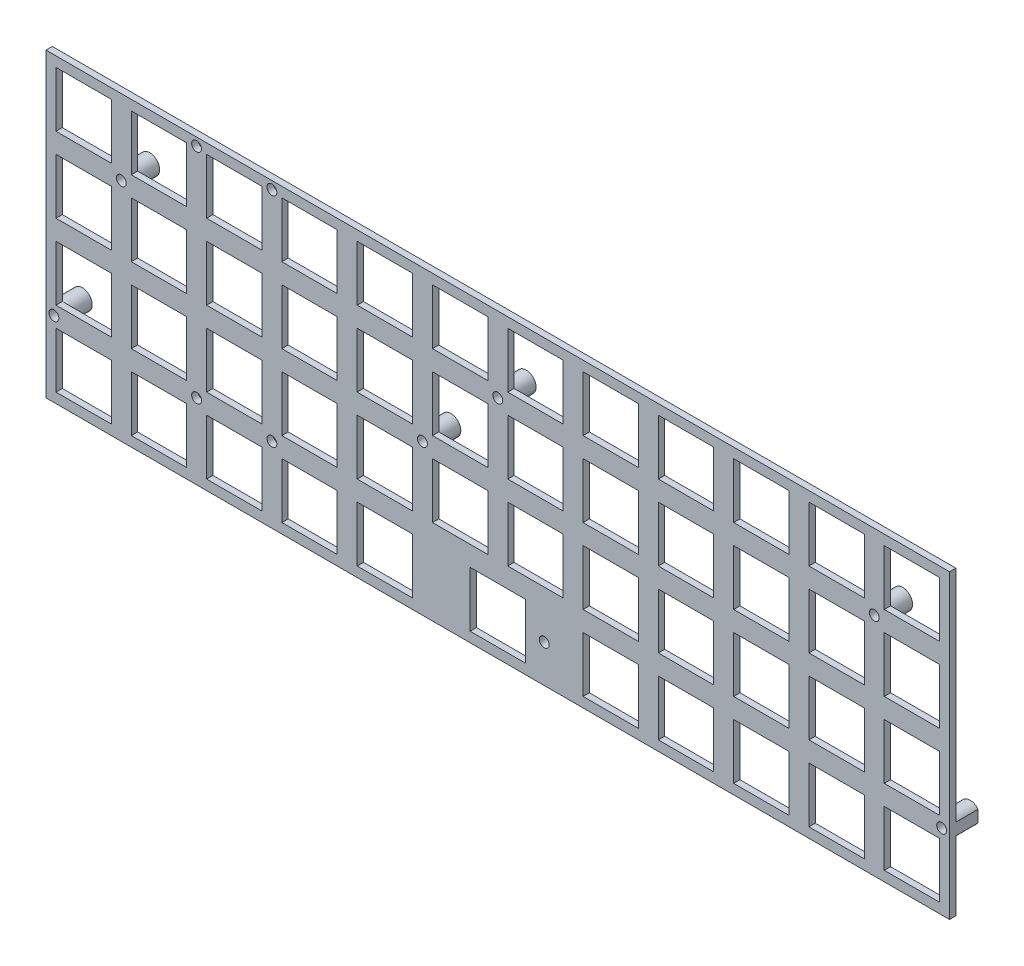
SolidWorks part; units mm, degrees
ref_plane "Alzado" through (0, 0, 0) normal (0, 0, 1) x (1, 0, 0)
ref_plane "Planta" through (0, 0, 0) normal (0, 1, 0) x (1, 0, 0)
ref_plane "Vista lateral" through (0, 0, 0) normal (1, 0, 0) x (0, 0, -1)
sketch "Croquis1" plane through (0, 0, 0) normal (0, 0, 1) x (1, 0, 0)
  line L1 (0, 0) -> (228.6, 0)
  line L2 (0, 0) -> (0, 76.2)
  line L3 (0, 76.2) -> (228.6, 76.2)
  line L4 (228.6, 0) -> (228.6, 76.2)
  dimension "D1" = 76.2
  dimension "D2" = 228.6
extrude "Saliente-Extruir1" add sketch "Croquis1" along normal blind 1.6
sketch "Croquis2" plane through (0, 0, 1.6) normal (0, 0, 1) x (1, 0, 0)
  line L0 (0, 57.15) -> (19.05, 76.2) construction
  line L1 (0, 76.2) -> (19.05, 76.2) construction
  line L2 (0, 76.2) -> (0, 57.15) construction
  line L3 (0, 57.15) -> (19.05, 57.15) construction
  line L4 (19.05, 76.2) -> (19.05, 57.15) construction
  line L5 (21.575, 59.675) -> (21.575, 73.675)
  line L6 (2.525, 59.675) -> (16.525, 59.675)
  line L7 (2.525, 59.675) -> (2.525, 73.675)
  line L8 (2.525, 73.675) -> (16.525, 73.675)
  line L9 (16.525, 59.675) -> (16.525, 73.675)
  line L10 (2.525, 59.675) -> (16.525, 73.675) construction
  line L11 (2.525, 73.675) -> (16.525, 59.675) construction
  line L12 (21.575, 59.675) -> (35.575, 59.675)
  line L13 (35.575, 59.675) -> (35.575, 73.675)
  line L14 (21.575, 73.675) -> (35.575, 73.675)
  line L15 (40.625, 59.675) -> (40.625, 73.675)
  line L16 (40.625, 59.675) -> (54.625, 59.675)
  line L17 (54.625, 59.675) -> (54.625, 73.675)
  line L18 (40.625, 73.675) -> (54.625, 73.675)
  line L19 (59.675, 59.675) -> (59.675, 73.675)
  line L20 (59.675, 59.675) -> (73.675, 59.675)
  line L21 (73.675, 59.675) -> (73.675, 73.675)
  line L22 (59.675, 73.675) -> (73.675, 73.675)
  line L23 (78.725, 59.675) -> (78.725, 73.675)
  line L24 (78.725, 59.675) -> (92.725, 59.675)
  line L25 (92.725, 59.675) -> (92.725, 73.675)
  line L26 (78.725, 73.675) -> (92.725, 73.675)
  line L27 (97.775, 59.675) -> (97.775, 73.675)
  line L28 (97.775, 59.675) -> (111.775, 59.675)
  line L29 (111.775, 59.675) -> (111.775, 73.675)
  line L30 (97.775, 73.675) -> (111.775, 73.675)
  line L31 (116.825, 59.675) -> (116.825, 73.675)
  line L32 (116.825, 59.675) -> (130.825, 59.675)
  line L33 (130.825, 59.675) -> (130.825, 73.675)
  line L34 (116.825, 73.675) -> (130.825, 73.675)
  line L35 (135.875, 59.675) -> (135.875, 73.675)
  line L36 (135.875, 59.675) -> (149.875, 59.675)
  line L37 (149.875, 59.675) -> (149.875, 73.675)
  line L38 (135.875, 73.675) -> (149.875, 73.675)
  line L39 (154.925, 59.675) -> (154.925, 73.675)
  line L40 (154.925, 59.675) -> (168.925, 59.675)
  line L41 (168.925, 59.675) -> (168.925, 73.675)
  line L42 (154.925, 73.675) -> (168.925, 73.675)
  line L43 (173.975, 59.675) -> (173.975, 73.675)
  line L44 (173.975, 59.675) -> (187.975, 59.675)
  line L45 (187.975, 59.675) -> (187.975, 73.675)
  line L46 (173.975, 73.675) -> (187.975, 73.675)
  line L47 (193.025, 59.675) -> (193.025, 73.675)
  line L48 (193.025, 59.675) -> (207.025, 59.675)
  line L49 (207.025, 59.675) -> (207.025, 73.675)
  line L50 (193.025, 73.675) -> (207.025, 73.675)
  line L51 (212.075, 59.675) -> (212.075, 73.675)
  line L52 (212.075, 59.675) -> (226.075, 59.675)
  line L53 (226.075, 59.675) -> (226.075, 73.675)
  line L54 (212.075, 73.675) -> (226.075, 73.675)
  line L55 (21.575, 40.625) -> (21.575, 54.625)
  line L56 (21.575, 40.625) -> (35.575, 40.625)
  line L57 (35.575, 40.625) -> (35.575, 54.625)
  line L58 (21.575, 54.625) -> (35.575, 54.625)
  line L59 (40.625, 40.625) -> (40.625, 54.625)
  line L60 (40.625, 40.625) -> (54.625, 40.625)
  line L61 (54.625, 40.625) -> (54.625, 54.625)
  line L62 (40.625, 54.625) -> (54.625, 54.625)
  line L63 (59.675, 40.625) -> (59.675, 54.625)
  line L64 (59.675, 40.625) -> (73.675, 40.625)
  line L65 (73.675, 40.625) -> (73.675, 54.625)
  line L66 (59.675, 54.625) -> (73.675, 54.625)
  line L67 (78.725, 40.625) -> (78.725, 54.625)
  line L68 (78.725, 40.625) -> (92.725, 40.625)
  line L69 (92.725, 40.625) -> (92.725, 54.625)
  line L70 (78.725, 54.625) -> (92.725, 54.625)
  line L71 (97.775, 40.625) -> (97.775, 54.625)
  line L72 (97.775, 40.625) -> (111.775, 40.625)
  line L73 (111.775, 40.625) -> (111.775, 54.625)
  line L74 (97.775, 54.625) -> (111.775, 54.625)
  line L75 (116.825, 40.625) -> (116.825, 54.625)
  line L76 (116.825, 40.625) -> (130.825, 40.625)
  line L77 (130.825, 40.625) -> (130.825, 54.625)
  line L78 (116.825, 54.625) -> (130.825, 54.625)
  line L79 (135.875, 40.625) -> (135.875, 54.625)
  line L80 (135.875, 40.625) -> (149.875, 40.625)
  line L81 (149.875, 40.625) -> (149.875, 54.625)
  line L82 (135.875, 54.625) -> (149.875, 54.625)
  line L83 (154.925, 40.625) -> (154.925, 54.625)
  line L84 (154.925, 40.625) -> (168.925, 40.625)
  line L85 (168.925, 40.625) -> (168.925, 54.625)
  line L86 (154.925, 54.625) -> (168.925, 54.625)
  line L87 (173.975, 40.625) -> (173.975, 54.625)
  line L88 (173.975, 40.625) -> (187.975, 40.625)
  line L89 (187.975, 40.625) -> (187.975, 54.625)
  line L90 (173.975, 54.625) -> (187.975, 54.625)
  line L91 (193.025, 40.625) -> (193.025, 54.625)
  line L92 (193.025, 40.625) -> (207.025, 40.625)
  line L93 (207.025, 40.625) -> (207.025, 54.625)
  line L94 (193.025, 54.625) -> (207.025, 54.625)
  line L95 (212.075, 40.625) -> (212.075, 54.625)
  line L96 (212.075, 40.625) -> (226.075, 40.625)
  line L97 (226.075, 40.625) -> (226.075, 54.625)
  line L98 (212.075, 54.625) -> (226.075, 54.625)
  line L99 (21.575, 21.575) -> (21.575, 35.575)
  line L100 (21.575, 21.575) -> (35.575, 21.575)
  line L101 (35.575, 21.575) -> (35.575, 35.575)
  line L102 (21.575, 35.575) -> (35.575, 35.575)
  line L103 (40.625, 21.575) -> (40.625, 35.575)
  line L104 (40.625, 21.575) -> (54.625, 21.575)
  line L105 (54.625, 21.575) -> (54.625, 35.575)
  line L106 (40.625, 35.575) -> (54.625, 35.575)
  line L107 (59.675, 21.575) -> (59.675, 35.575)
  line L108 (59.675, 21.575) -> (73.675, 21.575)
  line L109 (73.675, 21.575) -> (73.675, 35.575)
  line L110 (59.675, 35.575) -> (73.675, 35.575)
  line L111 (78.725, 21.575) -> (78.725, 35.575)
  line L112 (78.725, 21.575) -> (92.725, 21.575)
  line L113 (92.725, 21.575) -> (92.725, 35.575)
  line L114 (78.725, 35.575) -> (92.725, 35.575)
  line L115 (97.775, 21.575) -> (97.775, 35.575)
  line L116 (97.775, 21.575) -> (111.775, 21.575)
  line L117 (111.775, 21.575) -> (111.775, 35.575)
  line L118 (97.775, 35.575) -> (111.775, 35.575)
  line L119 (116.825, 21.575) -> (116.825, 35.575)
  line L120 (116.825, 21.575) -> (130.825, 21.575)
  line L121 (130.825, 21.575) -> (130.825, 35.575)
  line L122 (116.825, 35.575) -> (130.825, 35.575)
  line L123 (135.875, 21.575) -> (135.875, 35.575)
  line L124 (135.875, 21.575) -> (149.875, 21.575)
  line L125 (149.875, 21.575) -> (149.875, 35.575)
  line L126 (135.875, 35.575) -> (149.875, 35.575)
  line L127 (154.925, 21.575) -> (154.925, 35.575)
  line L128 (154.925, 21.575) -> (168.925, 21.575)
  line L129 (168.925, 21.575) -> (168.925, 35.575)
  line L130 (154.925, 35.575) -> (168.925, 35.575)
  line L131 (173.975, 21.575) -> (173.975, 35.575)
  line L132 (173.975, 21.575) -> (187.975, 21.575)
  line L133 (187.975, 21.575) -> (187.975, 35.575)
  line L134 (173.975, 35.575) -> (187.975, 35.575)
  line L135 (193.025, 21.575) -> (193.025, 35.575)
  line L136 (193.025, 21.575) -> (207.025, 21.575)
  line L137 (207.025, 21.575) -> (207.025, 35.575)
  line L138 (193.025, 35.575) -> (207.025, 35.575)
  line L139 (212.075, 21.575) -> (212.075, 35.575)
  line L140 (212.075, 21.575) -> (226.075, 21.575)
  line L141 (226.075, 21.575) -> (226.075, 35.575)
  line L142 (212.075, 35.575) -> (226.075, 35.575)
  line L143 (21.575, 2.525) -> (21.575, 16.525)
  line L144 (21.575, 2.525) -> (35.575, 2.525)
  line L145 (35.575, 2.525) -> (35.575, 16.525)
  line L146 (21.575, 16.525) -> (35.575, 16.525)
  line L147 (40.625, 2.525) -> (40.625, 16.525)
  line L148 (40.625, 2.525) -> (54.625, 2.525)
  line L149 (54.625, 2.525) -> (54.625, 16.525)
  line L150 (40.625, 16.525) -> (54.625, 16.525)
  line L151 (59.675, 2.525) -> (59.675, 16.525)
  line L152 (59.675, 2.525) -> (73.675, 2.525)
  line L153 (73.675, 2.525) -> (73.675, 16.525)
  line L154 (59.675, 16.525) -> (73.675, 16.525)
  line L155 (78.725, 2.525) -> (78.725, 16.525)
  line L156 (78.725, 2.525) -> (92.725, 2.525)
  line L157 (92.725, 2.525) -> (92.725, 16.525)
  line L158 (78.725, 16.525) -> (92.725, 16.525)
  line L159 (97.775, 2.525) -> (97.775, 16.525) construction
  line L160 (97.775, 2.525) -> (111.775, 2.525) construction
  line L161 (111.775, 2.525) -> (111.775, 16.525) construction
  line L162 (97.775, 16.525) -> (111.775, 16.525) construction
  line L163 (116.825, 2.525) -> (116.825, 16.525) construction
  line L164 (116.825, 2.525) -> (130.825, 2.525) construction
  line L165 (130.825, 2.525) -> (130.825, 16.525) construction
  line L166 (116.825, 16.525) -> (130.825, 16.525) construction
  line L167 (135.875, 2.525) -> (135.875, 16.525)
  line L168 (135.875, 2.525) -> (149.875, 2.525)
  line L169 (149.875, 2.525) -> (149.875, 16.525)
  line L170 (135.875, 16.525) -> (149.875, 16.525)
  line L171 (154.925, 2.525) -> (154.925, 16.525)
  line L172 (154.925, 2.525) -> (168.925, 2.525)
  line L173 (168.925, 2.525) -> (168.925, 16.525)
  line L174 (154.925, 16.525) -> (168.925, 16.525)
  line L175 (173.975, 2.525) -> (173.975, 16.525)
  line L176 (173.975, 2.525) -> (187.975, 2.525)
  line L177 (187.975, 2.525) -> (187.975, 16.525)
  line L178 (173.975, 16.525) -> (187.975, 16.525)
  line L179 (193.025, 2.525) -> (193.025, 16.525)
  line L180 (193.025, 2.525) -> (207.025, 2.525)
  line L181 (207.025, 2.525) -> (207.025, 16.525)
  line L182 (193.025, 16.525) -> (207.025, 16.525)
  line L183 (212.075, 2.525) -> (212.075, 16.525)
  line L184 (212.075, 2.525) -> (226.075, 2.525)
  line L185 (226.075, 2.525) -> (226.075, 16.525)
  line L186 (212.075, 16.525) -> (226.075, 16.525)
  line L187 (2.525, 40.625) -> (2.525, 54.625)
  line L188 (2.525, 40.625) -> (16.525, 40.625)
  line L189 (16.525, 40.625) -> (16.525, 54.625)
  line L190 (2.525, 54.625) -> (16.525, 54.625)
  line L191 (2.525, 21.575) -> (2.525, 35.575)
  line L192 (2.525, 21.575) -> (16.525, 21.575)
  line L193 (16.525, 21.575) -> (16.525, 35.575)
  line L194 (2.525, 35.575) -> (16.525, 35.575)
  line L195 (2.525, 2.525) -> (2.525, 16.525)
  line L196 (2.525, 2.525) -> (16.525, 2.525)
  line L197 (16.525, 2.525) -> (16.525, 16.525)
  line L198 (2.525, 16.525) -> (16.525, 16.525)
  line L199 (2.525, 59.675) -> (21.575, 59.675) construction
  line L200 (2.525, 59.675) -> (2.525, 40.625) construction
  line L201 (111.775, 9.525) -> (116.825, 9.525) construction
  line L203 (107.3, 2.525) -> (121.3, 2.525)
  line L204 (107.3, 2.525) -> (107.3, 16.525)
  line L205 (107.3, 16.525) -> (121.3, 16.525)
  line L206 (121.3, 2.525) -> (121.3, 16.525)
  line L207 (107.3, 2.525) -> (121.3, 16.525) construction
  line L208 (107.3, 16.525) -> (121.3, 2.525) construction
  point P5 (9.525, 66.675)
  point P203 (114.3, 9.525)
  dimension "D1" = 14
  dimension "D2" = 19.05
  dimension "D5" = 19.05
  dimension "D6" = 19.05
  dimension "D3" = 12
  dimension "D4" = 4
extrude "Cortar-Extruir1" cut sketch "Croquis2" against normal through all
sketch "Croquis3" plane through (0, 0, 1.6) normal (0, 0, 1) x (1, 0, 0)
  line L0 (92.725, 35.575) -> (97.775, 40.625) construction
  line L1 (207.025, 54.625) -> (212.075, 59.675) construction
  line L2 (16.525, 54.625) -> (21.575, 59.675) construction
  line L3 (111.775, 59.675) -> (116.825, 54.625) construction
  line L9 (2.525, 21.575) -> (2.525, 16.525) construction
  line L10 (2.525, 19.05) -> (0, 19.05) construction
  line L11 (0, 76.2) -> (0, 0) construction
  line L16 (2.525, 19.05) -> (228.6, 19.05) construction
  line L17 (228.6, 0) -> (228.6, 76.2) construction
  line L22 (130.825, 21.575) -> (130.825, 0) construction
  line L23 (0, 0) -> (228.6, 0) construction
  line L24 (121.3, 9.525) -> (130.825, 9.525) construction
  line L25 (121.3, 2.525) -> (121.3, 16.525) construction
  circle A0 centre (2, 19.05) radius 1.25
  circle A1 centre (226.6, 19.05) radius 1.25
  circle A2 centre (126.0625, 9.525) radius 1.25
  circle A4 centre (95.25, 38.1) radius 1.25
  circle A5 centre (209.55, 57.15) radius 1.25
  circle A6 centre (19.05, 57.15) radius 1.25
  circle A7 centre (114.3, 57.15) radius 1.25
  dimension "D1" = 2.5
  dimension "D2" = 2
  dimension "D3" = 2
  dimension "D4" = 19.05
  dimension "D5" = 9.525
  dimension "D6" = 38.1
  dimension "D7" = 57.15
  dimension "D8" = 19.05
  dimension "D9" = 95.25
  dimension "D10" = 114.3
  dimension "D11" = 126.0625
  dimension "D12" = 209.55
  dimension "D13" = 226.6
  dimension "D14" = 2
extrude "Cortar-Extruir2" cut sketch "Croquis3" against normal through all both and the other way through all
sketch "Croquis4" plane through (0, 0, 0) normal (0, 0, -1) x (-1, 0, 0)
  line L0 (-228.6, 17.55) -> (-228.6, 20.55)
  line L2 (-228.6, 0) -> (-228.6, 76.2) construction
  line L3 (0, 17.55) -> (0, 20.55)
  line L5 (0, 76.2) -> (0, 0) construction
  arc A0 (-228.6, 17.55) -> (-228.6, 20.55) centre (-226.6, 19.05) ccw
  circle A1 centre (-209.55, 57.15) radius 2.5
  circle A2 centre (-126.0625, 9.525) radius 2.5
  circle A3 centre (-95.25, 38.1) radius 2.5
  circle A4 centre (-19.05, 57.15) radius 2.5
  arc A5 (0, 20.55) -> (0, 17.55) centre (-2, 19.05) ccw
  circle A6 centre (-114.3, 57.15) radius 2.5
  circle A7 centre (-226.6, 19.05) radius 1.25 construction
  circle A8 centre (-209.55, 57.15) radius 1.25 construction
  circle A9 centre (-19.05, 57.15) radius 1.25 construction
  circle A10 centre (-2, 19.05) radius 1.25 construction
  circle A11 centre (-126.0625, 9.525) radius 1.25 construction
  circle A12 centre (-95.25, 38.1) radius 1.25 construction
  circle A13 centre (-114.3, 57.15) radius 1.25 construction
  circle A14 centre (-226.6, 19.05) radius 1.25
  circle A15 centre (-209.55, 57.15) radius 1.25
  circle A16 centre (-19.05, 57.15) radius 1.25
  circle A17 centre (-2, 19.05) radius 1.25
  circle A18 centre (-126.0625, 9.525) radius 1.25
  circle A19 centre (-95.25, 38.1) radius 1.25
  circle A20 centre (-114.3, 57.15) radius 1.25
  dimension "D1" = 5
extrude "Saliente-Extruir2" add sketch "Croquis4" along normal blind 5.6
sketch "Croquis5" plane through (0, 0, 1.6) normal (0, 0, 1) x (1, 0, 0)
  line L0 (35.575, 59.675) -> (40.625, 59.675) construction
  line L3 (54.625, 59.675) -> (59.675, 59.675) construction
  line L4 (38.1, 59.675) -> (38.1, 76.2) construction
  line L5 (228.6, 76.2) -> (0, 76.2) construction
  line L6 (54.625, 16.525) -> (59.675, 21.575) construction
  line L7 (35.575, 21.575) -> (40.625, 16.525) construction
  line L8 (57.15, 59.675) -> (57.15, 76.2) construction
  line L9 (38.1, 74.2) -> (57.15, 74.2) construction
  circle A0 centre (38.1, 19.05) radius 1.25
  circle A1 centre (57.15, 19.05) radius 1.25
  circle A4 centre (38.1, 74.2) radius 1.25
  circle A5 centre (57.15, 74.2) radius 1.25
  circle A6 centre (19.05, 57.15) radius 1.25 construction
  dimension "D1" = 2
extrude "Cortar-Extruir3" cut sketch "Croquis5" against normal through all both and the other way through all
